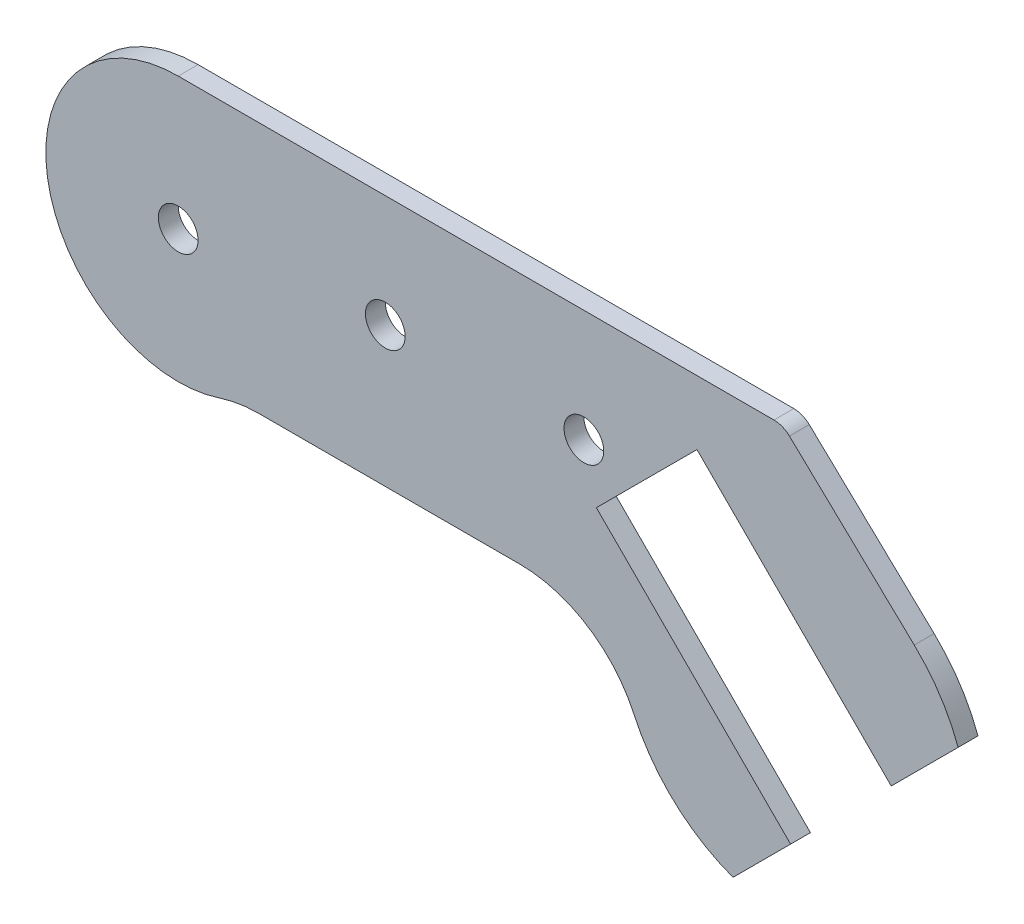
SolidWorks part; units mm, degrees
material "Beech"
ref_plane "Front Plane" through (0, 0, 0) normal (0, 0, 1) x (1, 0, 0)
ref_plane "Top Plane" through (0, 0, 0) normal (0, 1, 0) x (1, 0, 0)
ref_plane "Right Plane" through (0, 0, 0) normal (1, 0, 0) x (0, 0, -1)
sketch "Sketch1" plane through (0, 0, 0) normal (0, 0, 1) x (1, 0, 0)
  line L14 (77.0876, 14.7614) -> (61.8849, -0.4414)
  line L16 (50.3022, -13.6086) -> (10.8971, -13.6086)
  line L17 (116.5418, -4.4743) -> (106.4326, -14.5835)
  line L18 (77.0876, 14.7614) -> (106.4326, -14.5835)
  line L22 (61.8849, -0.4414) -> (91.2298, -29.7863)
  line L23 (91.0571, 23.5089) -> (109.9128, 5.6074)
  line L24 (91.2298, -29.7863) -> (82.5348, -38.4813)
  line L25 (-1.283, 24.4428) -> (88.717, 24.4428)
  arc A9 (50.3022, -13.6086) -> (67.6, -24.6884) centre (50.3022, -32.6511) cw
  circle A10 centre (30, 7.5) radius 3
  arc A11 (67.6, -24.6884) -> (82.5348, -38.4813) centre (91.6691, -13.6086) ccw
  arc A12 (-1.283, 24.4428) -> (4.9564, -14.559) centre (-1.283, 4.4428) ccw
  arc A13 (10.8971, -13.6086) -> (4.9564, -14.559) centre (10.8971, -32.6511) ccw
  circle A14 centre (-1.283, 4.4428) radius 3
  arc A15 (91.0571, 23.5089) -> (88.717, 24.4428) centre (88.717, 21.0441) ccw
  arc A16 (116.5418, -4.4743) -> (109.9128, 5.6074) centre (91.6691, -13.6086) ccw
  circle A17 centre (60, 7.5) radius 3
  point P8 (194.6466, 18.904)
  point P21 (115, -10)
  point P26 (132.2218, -2.2218)
  point P38 (145.985, 14.178)
  point P55 (99.1664, -1.6664)
  dimension "D1" = 90
  dimension "D3" = 26
  dimension "D7" = 21.5
  dimension "D4" = 30
  dimension "D5" = 6
  dimension "D6" = 20
  dimension "D2" = 41.5
extrude "Boss-Extrude1" add sketch "Sketch1" along normal blind 3
